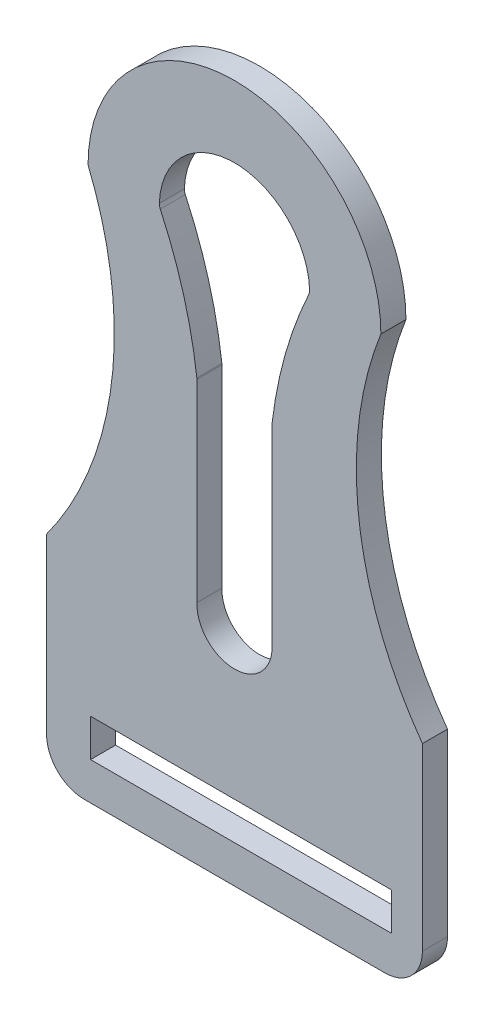
SolidWorks part; units mm, degrees
other "DetailItem1"
ref_plane "Frontal" through (0, 0, 0) normal (0, 0, 1) x (1, 0, 0)
ref_plane "Horizontal" through (0, 0, 0) normal (0, 1, 0) x (1, 0, 0)
ref_plane "Profile" through (0, 0, 0) normal (1, 0, 0) x (0, 0, -1)
sketch "Sketch1" plane through (0, 0, 0) normal (0, 0, 1) x (1, 0, 0)
  line L0 (0, 62.7307) -> (0, -57.805) construction
  line L1 (0, 24.745) -> (0, -57.805) construction
  line L2 (-9.5201, -57.4997) -> (-9.5201, -8.5084)
  line L3 (9.525, -8.8087) -> (9.525, -57.805)
  line L4 (0, 24.745) -> (0, -114.955) construction
  line L5 (47.625, -59.8747) -> (47.625, -105.43)
  line L6 (-47.625, -61.5237) -> (-47.625, -105.43)
  line L7 (-38.1, -114.955) -> (38.1, -114.955)
  line L8 (-36.4663, -105.43) -> (39.7337, -105.43)
  line L9 (39.7337, -105.43) -> (39.7337, -95.905)
  line L10 (39.7337, -95.905) -> (-36.4663, -95.905)
  line L11 (-36.4663, -95.905) -> (-36.4663, -105.43)
  arc A0 (-47.625, -105.43) -> (-38.1, -114.955) centre (-38.1, -105.43) ccw
  arc A1 (-37.1033, 24.745) -> (37.1033, 24.745) centre (0, 24.745) cw
  arc A2 (9.525, -57.805) -> (-9.5201, -57.4997) centre (0, -57.805) cw
  arc A3 (-9.5388, -8.2004) -> (-18.8042, 24.22) centre (-116.6924, -21.2894) ccw
  arc A4 (19.0396, 25.373) -> (-19.0396, 25.3748) centre (0, 24.745) ccw
  arc A5 (18.8055, 24.2212) -> (9.5425, -8.5107) centre (116.7474, -21.1726) ccw
  arc A6 (-19.0396, 25.3748) -> (-18.8042, 24.22) centre (-16.501, 25.2908) ccw
  arc A7 (19.0396, 25.373) -> (18.8055, 24.2212) centre (16.501, 25.2893) cw
  arc A8 (-9.5201, -8.5084) -> (-9.5388, -8.2004) centre (-12.0601, -8.5084) ccw
  arc A9 (9.5425, -8.5107) -> (9.525, -8.8087) centre (12.065, -8.8087) ccw
  arc A10 (-37.1033, 24.745) -> (-47.625, -61.5237) centre (-119.3498, -8.9998) cw
  arc A11 (37.1033, 24.745) -> (47.625, -59.8747) centre (119.7771, -7.9392) ccw
  arc A12 (38.1, -114.955) -> (47.625, -105.43) centre (38.1, -105.43) ccw
  point P28 (-47.625, -114.955)
  point P38 (47.625, -114.955)
  dimension "D2" = 82.55
  dimension "D3" = 139.7
  dimension "D8" = 88.9
  dimension "D9" = 9.525
  dimension "D4" = 95.25
  dimension "D5" = 9.525
  dimension "D6" = 76.2
  dimension "D7" = 9.525
extrude "Extrude1" add sketch "Sketch1" along normal blind 6.35
